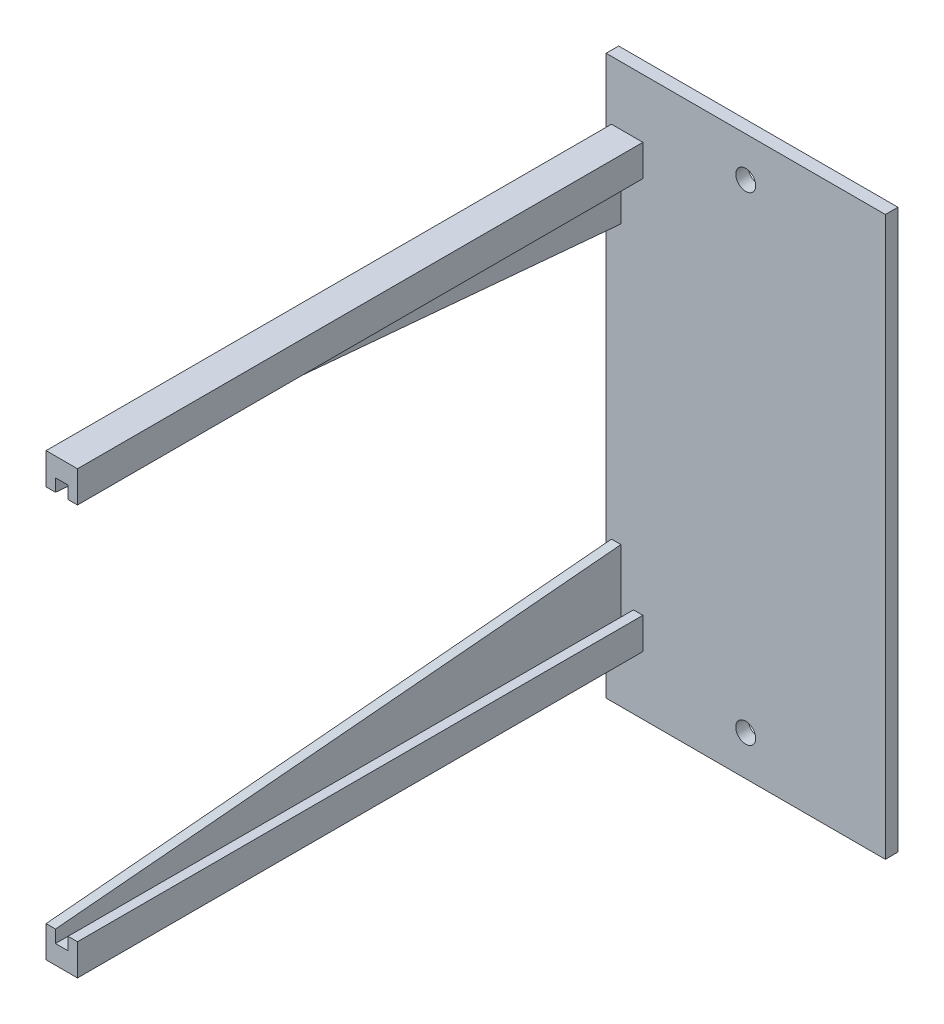
SolidWorks part; units mm, degrees
ref_plane "Front Plane" through (0, 0, 0) normal (0, 0, 1) x (1, 0, 0)
ref_plane "Top Plane" through (0, 0, 0) normal (0, 1, 0) x (1, 0, 0)
ref_plane "Right Plane" through (0, 0, 0) normal (1, 0, 0) x (0, 0, -1)
sketch "Front Face" plane through (0, 0, 0) normal (0, 0, 1) x (1, 0, 0)
  line L0 (0, 38.1) -> (0, -38.1) construction
  line L1 (-22.225, 44.45) -> (22.225, 44.45)
  line L2 (-22.225, 44.45) -> (-22.225, -44.45)
  line L3 (-22.225, -44.45) -> (22.225, -44.45)
  line L4 (22.225, 44.45) -> (22.225, -44.45)
  line L5 (0, 38.1) -> (0, 44.45) construction
  line L6 (0, -38.1) -> (0, -44.45) construction
  line L7 (0, -48.895) -> (0, 48.895) construction
  line L8 (24.4475, 0) -> (-24.4475, 0) construction
  line L9 (-22.225, 35.1) -> (22.225, 35.1) construction
  circle A0 centre (0, 38.1) radius 1.5875
  circle A1 centre (0, -38.1) radius 1.5875
  point P12 (0, 0)
  dimension "D1" = 3.175
  dimension "D2" = 88.9
  dimension "D3" = 76.2
  dimension "D4" = 3
  dimension "D5" = 44.45
extrude "Boss-Extrude1" add sketch "Front Face" along normal blind 2 contours L1 L4 L3 L2 | A0 | A1
ref_plane "Plane-FaceRear" through (0, 0, 2) normal (0, 0, 1) x (1, 0, 0)
sketch "Channel" plane through (0, 0, 2) normal (0, 0, 1) x (1, 0, 0)
  line L0 (-18.8683, 30.1) -> (-18.8683, -30.1) construction
  line L1 (-19.8683, 32.1) -> (-17.8683, 32.1)
  line L2 (-19.8683, 32.1) -> (-19.8683, 30.1)
  line L3 (-19.8683, 30.1) -> (-17.8683, 30.1)
  line L4 (-17.8683, 32.1) -> (-17.8683, 30.1)
  line L5 (-19.8683, -30.1) -> (-17.8683, -30.1)
  line L6 (-19.8683, -30.1) -> (-19.8683, -32.1)
  line L7 (-19.8683, -32.1) -> (-17.8683, -32.1)
  line L8 (-17.8683, -30.1) -> (-17.8683, -32.1)
  line L9 (-18.8683, 0) -> (22.225, 0) construction
  line L10 (22.225, 44.45) -> (22.225, -44.45) construction
  line L12 (-22.225, 35.1) -> (22.225, 35.1) construction
  line L13 (0, -48.895) -> (0, 48.895) construction
  dimension "D1" = 3
  dimension "D2" = 2
  dimension "D3" = 2
ref_plane "Plane-CantiArm" through (-18.8683, 0, 0) normal (-1, 0, 0) x (0, 0, 1)
sketch "CantiArm" plane through (-18.8683, 0, 0) normal (-1, 0, 0) x (0, 0, 1)
  line L0 (2, 35.1) -> (2, 30.1)
  line L1 (2, 30.1) -> (92, 30.1)
  line L2 (92, 30.1) -> (92, 35.1)
  line L3 (92, 35.1) -> (2, 35.1)
  line L4 (2, -24.4475) -> (2, 24.4475) construction
  dimension "D1" = 90
  dimension "D2" = 5
  dimension "D3" = 0
extrude "Boss-Extrude2" add sketch "CantiArm" along normal blind 2.5 and the other way blind 2.5
extrude "Cut-Extrude1" cut sketch "Channel" along normal through all contours L3 L4 L1 L2
sketch "Sketch5" plane through (-18.8683, 0, 0) normal (-1, 0, 0) x (0, 0, 1)
  line L0 (2, 22.1) -> (92, 30.1)
  line L1 (92, 30.1) -> (2, 30.1)
  line L2 (2, 30.1) -> (2, 22.1)
  line L3 (2, 35.1) -> (2, 30.1) construction
  line L4 (2, 30.1) -> (92, 30.1) construction
  dimension "D1" = 8
ref_plane "Plane3" through (-19.8683, 0, 0) normal (1, 0, 0) x (0, 0, -1)
extrude "Boss-Extrude5" add sketch "Sketch5" along normal up to surface (1.5 mm away) from surface at 1 up to face at (-21.3683, 32.6, 47) starting at plane "Plane3"
mirror "Mirror1" about plane through (0, 0, 0) normal (0, 1, 0) of "Boss-Extrude5", "Cut-Extrude1", "Boss-Extrude2"
equation "\"D1@Front Face\"=1/8*25.4"
equation "\"D2@Front Face\"=3.5*25.4"
equation "\"D5@Front Face\"=1.75*25.4"
